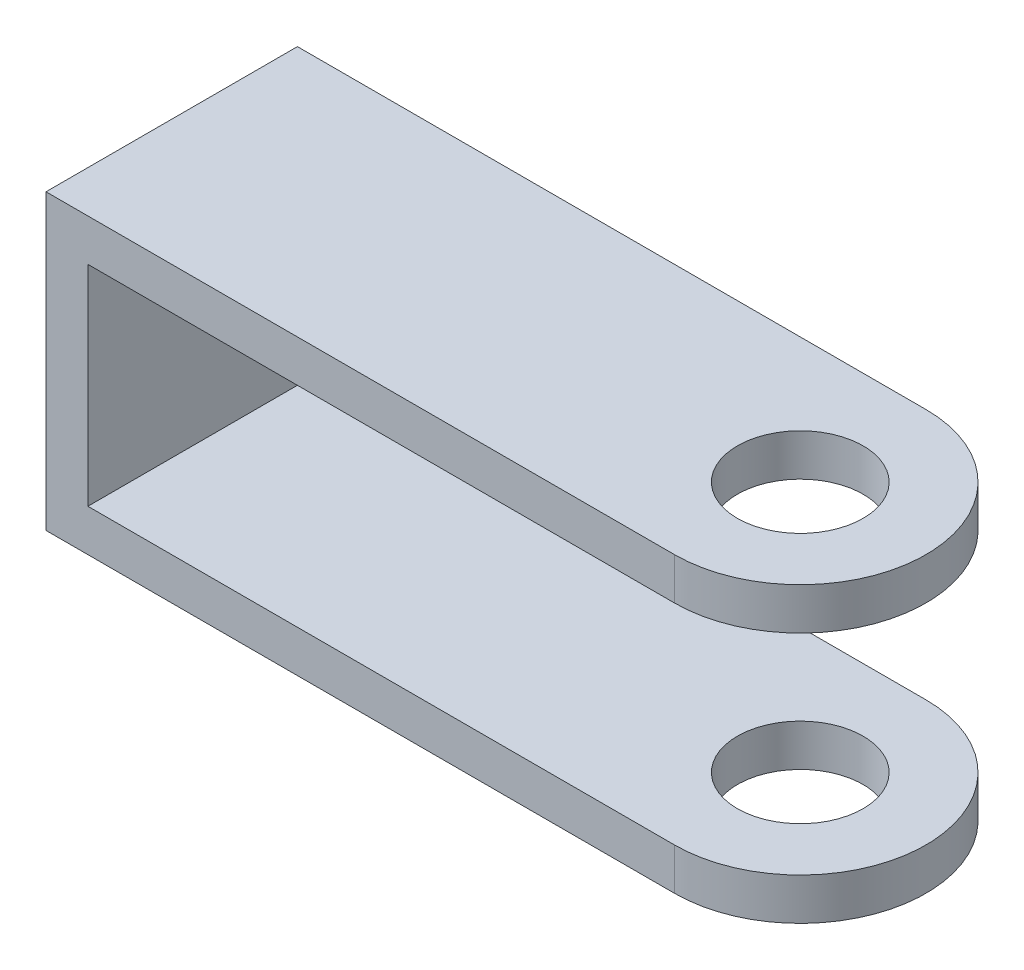
SolidWorks part; units mm, degrees
material "6063-O"
ref_plane "Front Plane" through (0, 0, 0) normal (0, 0, 1) x (1, 0, 0)
ref_plane "Top Plane" through (0, 0, 0) normal (0, 1, 0) x (1, 0, 0)
ref_plane "Right Plane" through (0, 0, 0) normal (1, 0, 0) x (0, 0, -1)
sketch "Sketch1" plane through (0, 0, 0) normal (0, 1, 0) x (1, 0, 0)
  line L0 (0, 30) -> (0, -30)
  line L1 (0, 30) -> (150, 30)
  line L2 (150, -30) -> (0, -30)
  arc A0 (150, 30) -> (150, -30) centre (150, 0) cw
  circle A1 centre (150, 0) radius 15
  dimension "D1" = 30
  dimension "D2" = 30
  dimension "D3" = 150
extrude "Boss-Extrude1" add sketch "Sketch1" along normal blind 10
sketch "Sketch2" plane through (0, 10, 0) normal (0, 1, 0) x (1, 0, 0)
  line L1 (0, -30) -> (10, -30)
  line L2 (0, -30) -> (0, 30)
  line L3 (0, 30) -> (10, 30)
  line L4 (10, -30) -> (10, 30)
  dimension "D1" = 10
extrude "Boss-Extrude2" add sketch "Sketch2" along normal blind 60
ref_plane "Plane1" through (0, 35, 0) normal (0, 1, 0) x (1, 0, 0)
mirror "Mirror2" about plane through (0, 35, 0) normal (0, 1, 0) of "Boss-Extrude1"
